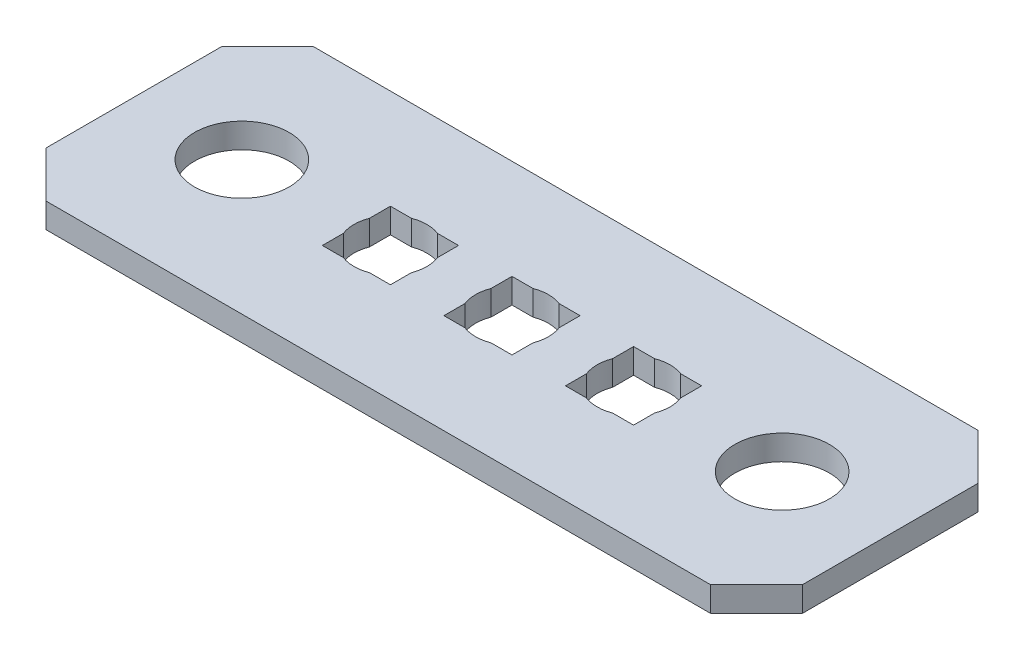
SolidWorks part; units mm, degrees
material "Custom Plastic"
ref_plane "Front Plane" through (0, 0, 0) normal (0, 0, 1) x (1, 0, 0)
ref_plane "Top Plane" through (0, 0, 0) normal (0, 1, 0) x (1, 0, 0)
ref_plane "Right Plane" through (0, 0, 0) normal (1, 0, 0) x (0, 0, -1)
ref_plane "Plane1" through (0, 0, 0) normal (0, -1, 0) x (1, 0, 0)
sketch "Sketch1" plane through (0, 0, 0) normal (0, -1, 0) x (1, 0, 0)
  line L0 (21.8948, -4.6863) -> (25.0952, -4.6863)
  line L1 (25.0952, -4.6863) -> (25.0952, -7.8867)
  line L2 (25.0952, -7.8867) -> (21.8948, -7.8867)
  line L3 (21.8948, -7.8867) -> (21.8948, -4.6863)
  line L4 (33.401, -12.573) -> (35.56, -10.414)
  line L5 (35.56, -10.414) -> (35.56, -2.159)
  line L6 (35.56, -2.159) -> (33.401, 0)
  line L7 (33.401, 0) -> (2.159, 0)
  line L8 (2.159, 0) -> (0, -2.159)
  line L9 (0, -2.159) -> (0, -10.414)
  line L10 (0, -10.414) -> (2.159, -12.573)
  line L11 (2.159, -12.573) -> (33.401, -12.573)
  line L12 (10.4648, -7.8867) -> (10.4648, -4.6863)
  line L13 (10.4648, -4.6863) -> (13.6652, -4.6863)
  line L14 (13.6652, -4.6863) -> (13.6652, -7.8867)
  line L15 (13.6652, -7.8867) -> (10.4648, -7.8867)
  line L16 (16.1798, -7.8867) -> (16.1798, -4.6863)
  line L17 (16.1798, -4.6863) -> (19.3802, -4.6863)
  line L18 (19.3802, -4.6863) -> (19.3802, -7.8867)
  line L19 (19.3802, -7.8867) -> (16.1798, -7.8867)
  circle A0 centre (5.08, -6.2865) radius 2.2225
  circle A1 centre (30.48, -6.2865) radius 2.2225
extrude "Boss-Extrude1" add sketch "Sketch1" against normal blind 1.1684
sketch "Sketch2" plane through (0, 1.1684, 0) normal (0, 1, 0) x (1, 0, 0)
  line L0 (10.4648, 6.2865) -> (13.6652, 6.2865) construction
  line L1 (10.4648, 4.6863) -> (10.4648, 7.8867) construction
  line L2 (13.6652, 7.8867) -> (13.6652, 4.6863) construction
  line L4 (16.1798, 4.6863) -> (16.1798, 7.8867) construction
  line L5 (16.1798, 6.2865) -> (19.3802, 6.2865) construction
  line L6 (19.3802, 7.8867) -> (19.3802, 4.6863) construction
  line L8 (21.8948, 4.6863) -> (21.8948, 7.8867) construction
  line L9 (21.8948, 6.2865) -> (25.0952, 6.2865) construction
  line L10 (25.0952, 7.8867) -> (25.0952, 4.6863) construction
  circle A0 centre (12.065, 6.2865) radius 1.7145
  circle A1 centre (17.78, 6.2865) radius 1.7145
  circle A2 centre (23.495, 6.2865) radius 1.7145
  dimension "D1" = 3.429
extrude "Cut-Extrude1" cut sketch "Sketch2" against normal blind 2.54
